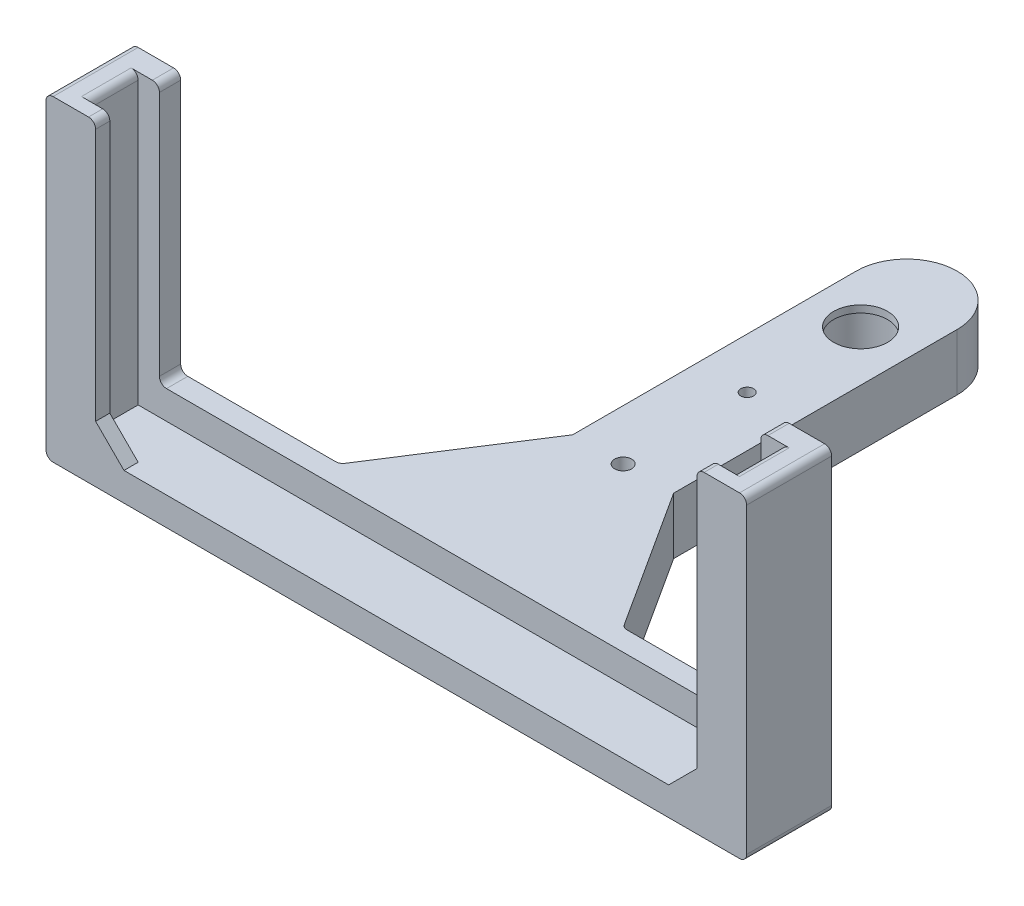
SolidWorks part; units mm, degrees
ref_plane "Front Plane" through (0, 0, 0) normal (0, 0, 1) x (1, 0, 0)
ref_plane "Top Plane" through (0, 0, 0) normal (0, 1, 0) x (1, 0, 0)
ref_plane "Right Plane" through (0, 0, 0) normal (1, 0, 0) x (0, 0, -1)
sketch "Sketch1" plane through (0, 0, 0) normal (0, 1, 0) x (1, 0, 0)
  line L0 (47.42, 0) -> (47.42, 6)
  line L1 (0, 0) -> (45.42, 0)
  line L3 (0, 6) -> (45.42, 6)
  line L6 (-2, 0) -> (-2, 6)
  line L8 (45.42, 6) -> (47.42, 6)
  line L9 (45.42, 0) -> (47.42, 0)
  line L10 (0, 6) -> (-2, 6)
  line L11 (0, 0) -> (-2, 0)
  line L12 (-2, -2) -> (-2, 8) construction
  line L13 (47.42, -2) -> (47.42, 8) construction
  line L14 (0, 0) -> (0, 6) construction
  line L15 (-2, 8) -> (47.42, 8) construction
  line L16 (45.42, 0) -> (45.42, 6) construction
  line L17 (-2, -2) -> (47.42, -2) construction
  dimension "D1" = 6
  dimension "D2" = 45.42
  dimension "D3" = 2
extrude "Boss-Extrude1" add sketch "Sketch1" along normal blind 22.34
sketch "Sketch3" plane through (0, 22.34, 0) normal (0, 1, 0) x (1, 0, 0)
  line L0 (47.42, 6) -> (-2, 6) construction
  line L1 (1.5, 6) -> (43.92, 6)
  line L2 (1.5, 6) -> (1.5, 0)
  line L3 (1.5, 0) -> (43.92, 0)
  line L4 (43.92, 6) -> (43.92, 0)
  line L5 (-2, 0) -> (47.42, 0) construction
  line L6 (-2, 6) -> (-2, 0) construction
  line L7 (47.42, 0) -> (47.42, 6) construction
  dimension "D1" = 3.5
  dimension "D2" = 3.5
extrude "Cut-Extrude1" cut sketch "Sketch3" against normal offset from surface (20.34 mm away) 2 up to face at (22.71, 0, -3)
sketch "Sketch4" plane through (0, 22.34, 0) normal (0, 1, 0) x (1, 0, 0)
  line L1 (0, 4.5) -> (45.42, 4.5)
  line L2 (0, 4.5) -> (0, 1)
  line L3 (0, 1) -> (45.42, 1)
  line L4 (45.42, 4.5) -> (45.42, 1)
  line L6 (1.5, 6) -> (-2, 6) construction
  dimension "D1" = 3.5
  dimension "D2" = 1.5
extrude "Cut-Extrude2" cut sketch "Sketch4" against normal offset from surface (20.34 mm away) 2 up to face at (22.71, 0, -3)
sketch "Sketch6" plane through (0, 0, 0) normal (0, -1, 0) x (1, 0, 0)
  line L1 (22.71, -32.75) -> (22.71, -24.75) construction
  line L4 (12.71, -6) -> (19.1461, -16)
  line L5 (47.42, -6) -> (-2, -6) construction
  line L6 (32.71, -6) -> (26.2739, -16)
  line L8 (26.2739, -16) -> (26.2739, -36)
  line L10 (19.1461, -36) -> (19.1461, -16)
  line L11 (22.71, -24.75) -> (22.71, -16) construction
  line L12 (47.42, 0) -> (-2, 0)
  line L13 (-2, 0) -> (-2, -6)
  line L14 (-2, -6) -> (47.42, -6)
  line L15 (47.42, -6) -> (47.42, 0)
  line L18 (12.71, -6) -> (32.71, -6)
  line L19 (22.71, -16) -> (22.71, -6) construction
  line L20 (-2, -6) -> (-2, 0) construction
  line L21 (47.42, 0) -> (47.42, -6) construction
  arc A2 (26.2739, -36) -> (19.1461, -36) centre (22.71, -36) cw
  circle A5 centre (22.71, -16) radius 0.6
  circle A6 centre (22.71, -24.75) radius 0.45
  circle A7 centre (22.71, -32.75) radius 2.25
  point P21 (22.71, -6)
  dimension "D7" = 1.2
  dimension "D8" = 0.9
  dimension "D9" = 8.75
  dimension "D12" = 16.75
  dimension "D13" = 4.5
  dimension "D4" = 10
  dimension "D5" = 10
  dimension "D10" = 20
  dimension "D11" = 0
  dimension "D14" = 7.1278
  dimension "D6" = 0
extrude "Boss-Extrude2" add sketch "Sketch6" against normal blind 4
sketch "Sketch7" plane through (0, 2, 0) normal (0, 1, 0) x (1, 0, 0)
  circle A0 centre (22.71, 32.75) radius 2.25
  circle A1 centre (22.71, 32.75) radius 1.9
  circle A3 centre (22.71, 32.75) radius 2.25 construction
extrude "Boss-Extrude3" add sketch "Sketch7" against normal blind 0.5 from surface at 2 starting at face at (22.71, 4, -35)
sketch "Sketch8" plane through (0, 2, 0) normal (0, 1, 0) x (1, 0, 0)
  line L1 (1.5, 6) -> (43.92, 6)
  line L2 (1.5, 6) -> (1.5, 4.5)
  line L3 (1.5, 4.5) -> (43.92, 4.5)
  line L4 (43.92, 6) -> (43.92, 4.5)
extrude "Boss-Extrude4" add sketch "Sketch8" along normal blind 2
sketch "Sketch11" plane through (0, 0, 0) normal (0, 0, 1) x (1, 0, 0)
  line L0 (1.5, 4) -> (3.5, 2)
  line L1 (1.5, 2) -> (43.92, 2) construction
  line L2 (43.92, 4) -> (41.92, 2)
  line L3 (1.5, 4) -> (1.5, 2)
  line L4 (1.5, 2) -> (3.5, 2)
  line L5 (43.92, 4) -> (43.92, 2)
  line L6 (43.92, 2) -> (41.92, 2)
extrude "Boss-Extrude5" add sketch "Sketch11" against normal up to surface (1 mm away) up to face at (0.75, 12.17, -1)
fillet "Fillet1" radius 0.5 14 edges at (1.5, 4, -5.25) (43.92, 4, -5.25) (47.42, 22.34, -3) (-2, 22.34, -3) (1.5, 22.34, -5.25) (43.92, 22.34, -0.5) (1.5, 22.34, -0.5) (43.92, 22.34, -5.25) (45.42, 22.34, -2.75) (0, 22.34, -2.75) (12.71, 2, -6) (32.71, 2, -6) (-2, 0, -3) (47.42, 0, -3)
